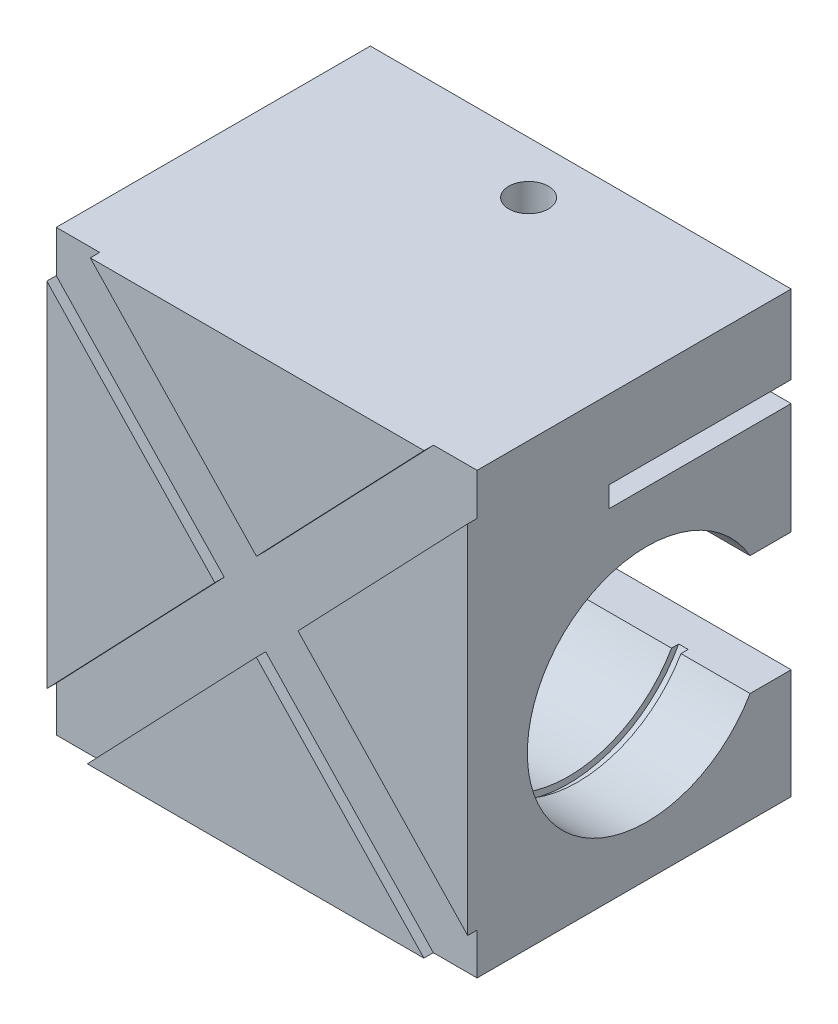
SolidWorks part; units mm, degrees
material "AISI 1020"
ref_plane "Front Plane" through (0, 0, 0) normal (0, 0, 1) x (1, 0, 0)
ref_plane "Top Plane" through (0, 0, 0) normal (0, 1, 0) x (1, 0, 0)
ref_plane "Right Plane" through (0, 0, 0) normal (1, 0, 0) x (0, 0, -1)
sketch "Sketch1" plane through (0, 0, 0) normal (1, 0, 0) x (0, 0, -1)
  line L0 (-23, 27) -> (51.3389, 27) construction
  line L1 (-50, 70) -> (0, 70)
  line L2 (-50, 70) -> (-50, 0)
  line L3 (-50, 0) -> (0, 0)
  line L4 (0, 70) -> (0, 0)
  line L5 (-6.5455, 36.5) -> (0, 36.5)
  line L6 (0, 36.5) -> (0, 17.5)
  line L7 (0, 17.5) -> (-6.5455, 17.5)
  line L8 (0, 57.5) -> (-29, 57.5)
  line L9 (-29, 57.5) -> (-29, 54.2)
  line L10 (-29, 54.2) -> (0, 54.2)
  line L11 (0, 54.2) -> (0, 57.5)
  arc A0 (-6.5455, 36.5) -> (-6.5455, 17.5) centre (-23, 27) ccw
  dimension "D4" = 38
  dimension "D1" = 50
  dimension "D2" = 70
  dimension "D3" = 27
  dimension "D5" = 27
  dimension "D6" = 9.5
  dimension "D7" = 12.5
  dimension "D8" = 3.3
  dimension "D9" = 29
extrude "Boss-Extrude1" add sketch "Sketch1" against normal blind 67 contours A0 L5 L4 L10 L9 L8 L1 L2 L3 L7
ref_plane "Plane1" through (-12.5, 0, 0) normal (1, 0, 0) x (0, 0, -1)
sketch "Sketch2" plane through (-12.5, 0, 0) normal (1, 0, 0) x (0, 0, -1)
  circle A0 centre (-23, 27) radius 20
  dimension "D1" = 40
extrude "Cut-Extrude1" cut sketch "Sketch2" along normal blind 1.5
ref_plane "Plane3" through (-33.5, 0, 0) normal (1, 0, 0) x (0, 0, -1)
mirror "Mirror1" about plane through (-33.5, 0, 0) normal (1, 0, 0) of "Cut-Extrude1"
sketch "Sketch7" plane through (0, 0, 50) normal (0, 0, 1) x (1, 0, 0)
  line L0 (-67, 0) -> (0, 70) construction
  line L1 (0, 70) -> (0, 0)
  line L2 (0, 0) -> (-67, 0)
  line L3 (-67, 70) -> (0, 0) construction
  line L4 (-67, 7.1492) -> (-40.262, 35.1298)
  line L5 (-67, 70) -> (-67, 0) construction
  line L6 (-67, 70) -> (0, 70) construction
  line L8 (0, 63.3677) -> (-27.0099, 35.1024)
  line L10 (-67, 63.3417) -> (-40.262, 35.1298)
  line L12 (0, 6.6036) -> (-27.0099, 35.1024)
  line L14 (-60.0843, 70) -> (-6.9406, 70)
  line L15 (0, 63.3677) -> (0, 6.6036)
  line L16 (-6.9676, 0) -> (-60.5533, 0)
  line L17 (-67, 63.3417) -> (-67, 7.1492)
  line L18 (-33.6218, 42.0787) -> (-60.0843, 70)
  line L19 (-33.6218, 42.0787) -> (-6.9406, 70)
  line L20 (-33.6502, 28.1535) -> (-60.5533, 0)
  line L21 (-33.6502, 28.1535) -> (-6.9676, 0)
  dimension "D1" = 9.6
  dimension "D2" = 9.6
extrude "Boss-Extrude3" add sketch "Sketch7" along normal blind 1.5
sketch "Sketch8" plane through (0, 70, 0) normal (0, 1, 0) x (1, 0, 0)
  line L0 (-67, -50) -> (-67, 0) construction
  line L2 (-67, 0) -> (0, 0) construction
  circle A0 centre (-33.5, -8.3) radius 3.15
  point P6 (-38.946, 0)
  dimension "D3" = 6.3
  dimension "D1" = 33.5
  dimension "D2" = 8.3
extrude "Cut-Extrude2" cut sketch "Sketch8" against normal blind 12.5
